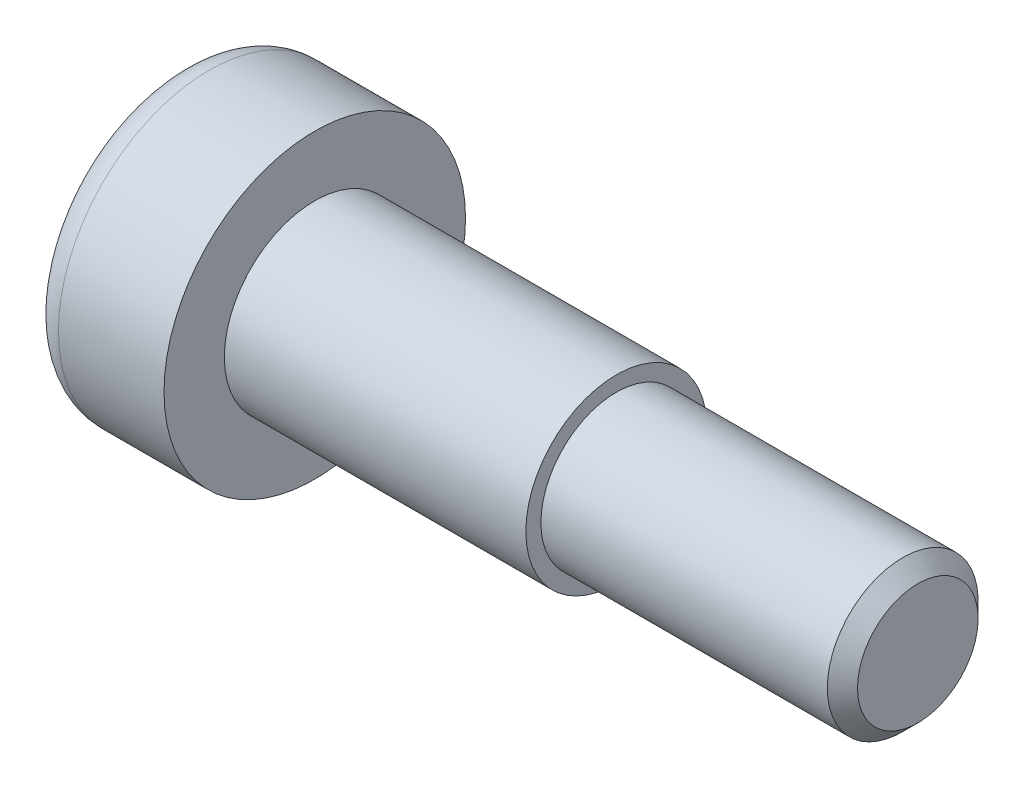
SolidWorks part; units mm, degrees
material "不锈钢 (铁素体)"
ref_plane "前视基准面" through (0, 0, 0) normal (0, 0, 1) x (1, 0, 0)
ref_plane "上视基准面" through (0, 0, 0) normal (0, 1, 0) x (1, 0, 0)
ref_plane "右视基准面" through (0, 0, 0) normal (1, 0, 0) x (0, 0, -1)
sketch "草图1" plane through (0, 0, 0) normal (0, 0, 1) x (1, 0, 0)
  line L0 (0, 0) -> (24.5, 0) construction
  line L1 (0, 0) -> (0, 5)
  line L2 (0, 5) -> (4.5, 5)
  line L3 (4.5, 5) -> (4.5, 3)
  line L4 (4.5, 3) -> (14.5, 3)
  line L5 (14.5, 3) -> (14.5, 2.5)
  line L6 (14.5, 2.5) -> (24.5, 2.5)
  line L7 (24.5, 2.5) -> (24.5, 0)
  line L8 (0, 0) -> (24.5, 0)
  dimension "D1" = 10
  dimension "D2" = 6
  dimension "D3" = 5
  dimension "D4" = 10
  dimension "D5" = 4.5
  dimension "D6" = 10
revolve "旋转1" add sketch "草图1" angle 360 about L0
cosmetic thread "装饰螺纹线1" parameters "D2"=4.134
sketch "草图2" plane through (0, 0, 0) normal (-1, 0, 0) x (0, 0, 1)
  line L0 (0, 0) -> (0, 1.7321) construction
  line L1 (0, 1.7321) -> (-1.5, 0.866)
  line L2 (-1.5, 0.866) -> (-1.5, -0.866)
  line L3 (-1.5, -0.866) -> (0, -1.7321)
  line L4 (0, -1.7321) -> (1.5, -0.866)
  line L5 (1.5, -0.866) -> (1.5, 0.866)
  line L6 (1.5, 0.866) -> (0, 1.7321)
  circle A0 centre (0, 0) radius 1.5 construction
  dimension "D1" = 3
extrude "切除-拉伸1" cut sketch "草图2" against normal blind 3
fillet "圆角1" radius 1 1 edges at (0, 0, 5)
chamfer "倒角1" distance 0.5 angle 45 1 edges at (24.5, 0, 2.5)
